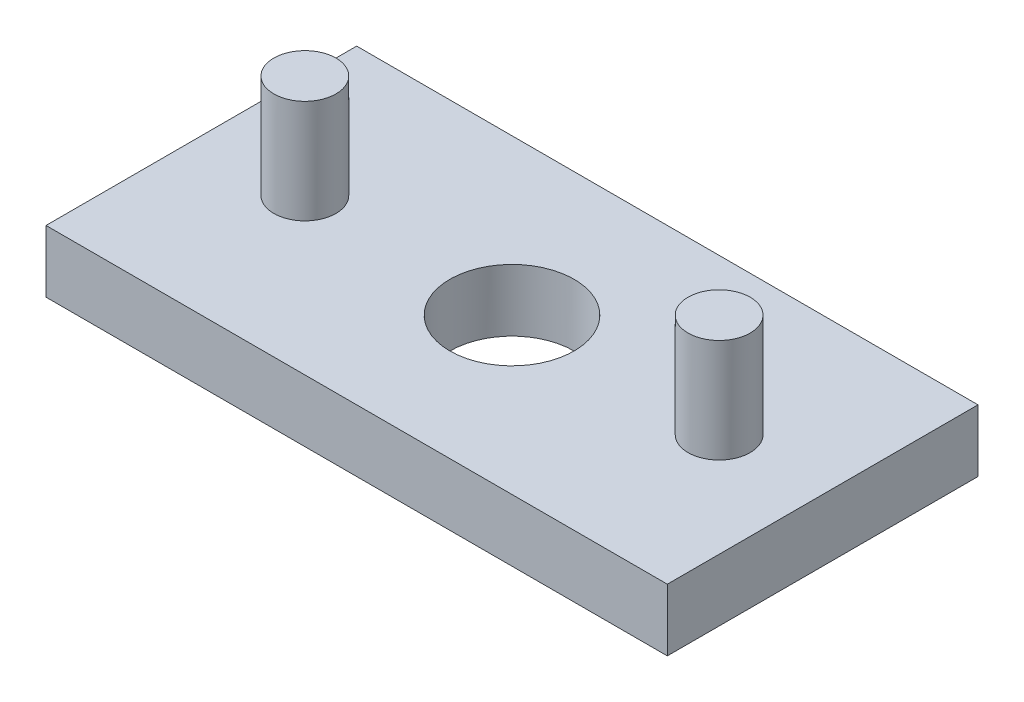
SolidWorks part; units mm, degrees
ref_plane "Front" through (0, 0, 0) normal (0, 0, 1) x (1, 0, 0)
ref_plane "Top" through (0, 0, 0) normal (0, 1, 0) x (1, 0, 0)
ref_plane "Right" through (0, 0, 0) normal (1, 0, 0) x (0, 0, -1)
sketch "草图1" plane through (0, 0, 0) normal (0, 1, 0) x (1, 0, 0)
  line L0 (-100, 0) -> (100, 0) construction
  line L1 (-150, -75) -> (150, -75)
  line L2 (-150, -75) -> (-150, 75)
  line L3 (-150, 75) -> (150, 75)
  line L4 (150, -75) -> (150, 75)
  line L5 (-150, -75) -> (150, 75) construction
  line L6 (-150, 75) -> (150, -75) construction
  line L7 (0, 42.3706) -> (0, -38.0109) construction
  point P0 (0, 0)
  point P10 (0, 0)
  dimension "D1" = 300
  dimension "D2" = 150
  dimension "D3" = 200
extrude "凸台-拉伸1" add sketch "草图1" along normal blind 30
sketch "草图2" plane through (0, 30, 0) normal (0, 1, 0) x (1, 0, 0)
  circle A0 centre (-100, 0) radius 15
  circle A1 centre (100, 0) radius 15
  point P4 (0, 0)
  point P6 (0, 0)
  point P7 (0, 0)
  dimension "D1" = 30
extrude "凸台-拉伸2" add sketch "草图2" along normal blind 50
sketch "草图3" plane through (0, 30, 0) normal (0, 1, 0) x (1, 0, 0)
  circle A0 centre (0, 0) radius 30
  dimension "D1" = 60
extrude "切除-拉伸1" cut sketch "草图3" against normal blind 50
